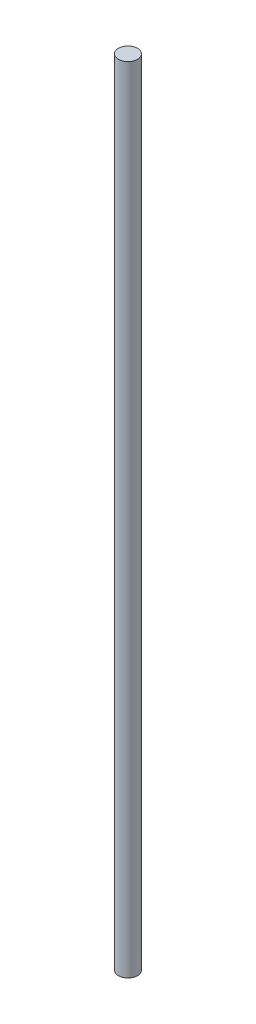
SolidWorks part; units mm, degrees
ref_plane "Alzado" through (0, 0, 0) normal (0, 0, 1) x (1, 0, 0)
ref_plane "Planta" through (0, 0, 0) normal (0, 1, 0) x (1, 0, 0)
ref_plane "Vista lateral" through (0, 0, 0) normal (1, 0, 0) x (0, 0, -1)
sketch "Croquis1" plane through (0, 0, 0) normal (0, 1, 0) x (1, 0, 0)
  circle A0 centre (0, 0) radius 4
  dimension "D1" = 8
extrude "Saliente-Extruir1" add sketch "Croquis1" along normal blind 332.21
